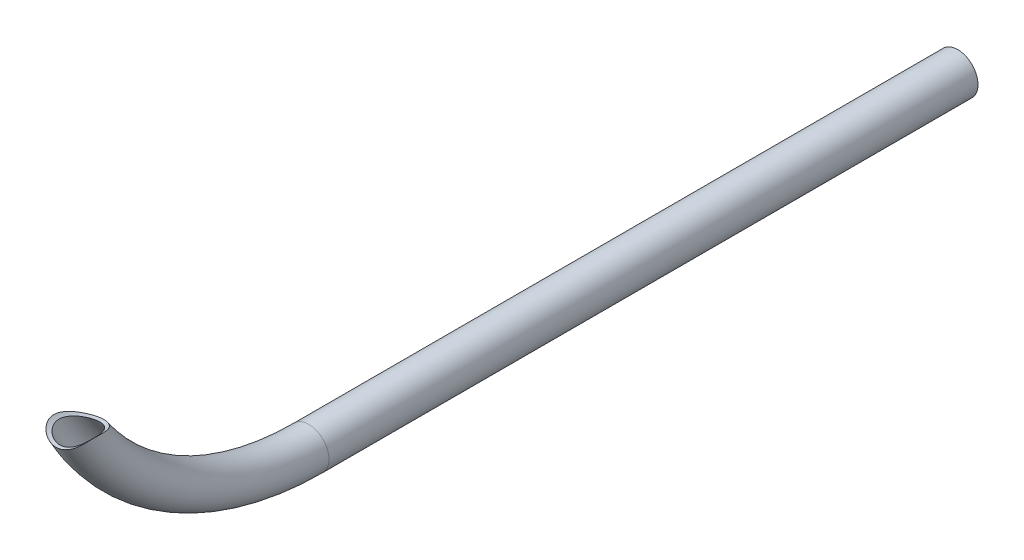
SolidWorks part; units mm, degrees
ref_plane "Front" through (0, 0, 0) normal (0, 0, 1) x (1, 0, 0)
ref_plane "Top" through (0, 0, 0) normal (0, 1, 0) x (1, 0, 0)
ref_plane "Right" through (0, 0, 0) normal (1, 0, 0) x (0, 0, -1)
sketch "Sketch2" plane through (0, 0, 0) normal (0, 0, 1) x (1, 0, 0)
  circle A0 centre (0, 0) radius 7.9375
  circle A1 centre (0, 0) radius 9.525
  dimension "D1" = 15.875
  dimension "D2" = 19.05
sketch "Sketch3" plane through (0, 0, 0) normal (1, 0, 0) x (0, 0, -1)
  line L0 (0, 0) -> (-304.8, 0)
  arc A0 (-304.8, 0) -> (-417.6556, 68.7538) centre (-304.8, 127) cw
  dimension "D1" = 127
  dimension "D2" = 304.8
sweep "Sweep1" add profiles "Sketch2" path "Sketch3"
sketch "Sketch5" plane through (0, 0, 395.0582) normal (0, 0, 1) x (1, 0, 0)
  circle A0 centre (0, 72.2312) radius 12.7 construction
  circle A1 centre (0, 72.2312) radius 12.7
extrude "Cut-Extrude2" cut sketch "Sketch5" along normal through all
